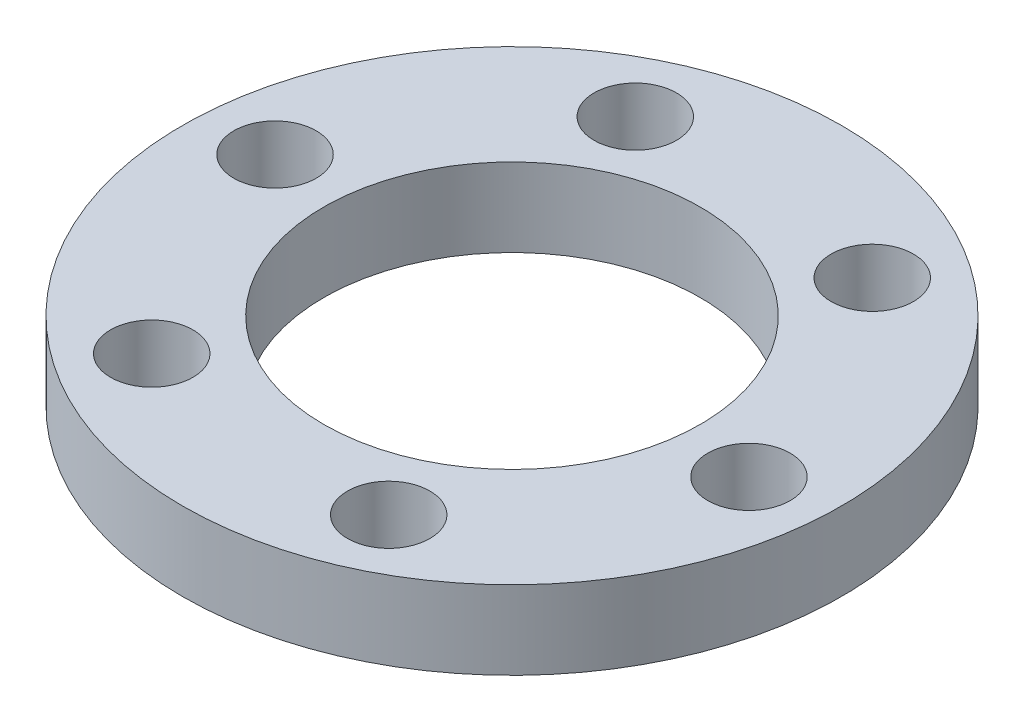
SolidWorks part; units mm, degrees
ref_plane "Front Plane" through (0, 0, 0) normal (0, 0, 1) x (1, 0, 0)
ref_plane "Top Plane" through (0, 0, 0) normal (0, 1, 0) x (1, 0, 0)
ref_plane "Right Plane" through (0, 0, 0) normal (1, 0, 0) x (0, 0, -1)
sketch "Sketch1" plane through (0, 0, 0) normal (0, 1, 0) x (1, 0, 0)
  circle A0 centre (0, 0) radius 21
  circle A1 centre (0, 0) radius 12
  circle A2 centre (0, 0) radius 16.5 construction
  circle A3 centre (-16.4451, 1.3448) radius 2.625
  circle A8 centre (-7.0579, 14.9143) radius 2.625
  circle A9 centre (9.3872, 13.5695) radius 2.625
  circle A10 centre (16.4451, -1.3448) radius 2.625
  circle A11 centre (7.0579, -14.9143) radius 2.625
  circle A12 centre (-9.3872, -13.5695) radius 2.625
  dimension "D1" = 42
  dimension "D2" = 33
  dimension "D3" = 24
  dimension "D4" = 5.25
  dimension "D5" = 6
extrude "Boss-Extrude1" add sketch "Sketch1" along normal blind 5 contours A1
